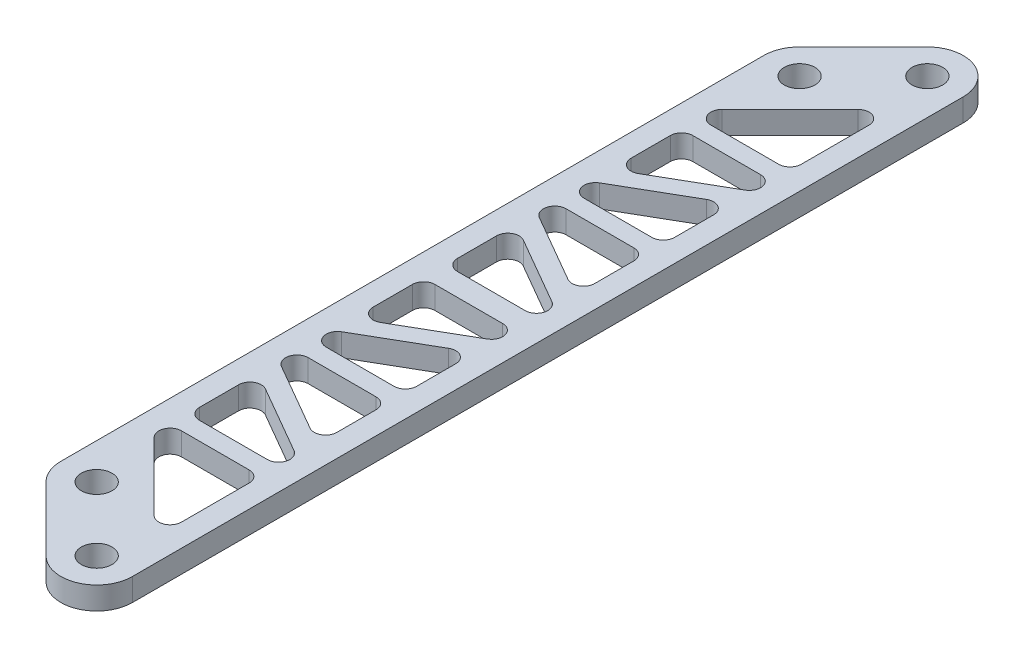
SolidWorks part; units mm, degrees
material "6061-T6 (SS)"
ref_plane "Front Plane" through (0, 0, 0) normal (0, 0, 1) x (1, 0, 0)
ref_plane "Top Plane" through (0, 0, 0) normal (0, 1, 0) x (1, 0, 0)
ref_plane "Right Plane" through (0, 0, 0) normal (1, 0, 0) x (0, 0, -1)
sketch "Sketch1" plane through (0, 0, 0) normal (0, 1, 0) x (1, 0, 0)
  line L0 (0, 0) -> (0, 49.3914)
  line L1 (1.4747, 52.9516) -> (10.4549, 61.9319)
  line L2 (19.05, 58.3717) -> (19.05, 0)
  line L3 (19.05, 0) -> (0, 0)
  line L4 (14.0151, 58.3717) -> (5.0349, 49.3914) construction
  line L5 (5.0349, 49.3914) -> (-44.3565, 0) construction
  line L6 (0, 0) -> (-44.3565, 0) construction
  line L7 (13.165, 49.4393) -> (3.64, 39.9143)
  line L8 (4.7625, 37.2042) -> (14.2875, 37.2042)
  line L9 (15.875, 38.7917) -> (15.875, 48.3167)
  line L13 (4.7625, 38.7917) -> (14.2875, 48.3167) construction
  arc A0 (10.4549, 61.9319) -> (19.05, 58.3717) centre (14.0151, 58.3717) cw
  arc A1 (0, 49.3914) -> (1.4747, 52.9516) centre (5.0349, 49.3914) cw
  circle A2 centre (14.0151, 58.3717) radius 2.0828
  circle A3 centre (5.0349, 49.3914) radius 2.0828
  arc A4 (3.64, 39.9143) -> (4.7625, 37.2042) centre (4.7625, 38.7917) ccw
  arc A5 (14.2875, 37.2042) -> (15.875, 38.7917) centre (14.2875, 38.7917) ccw
  arc A6 (13.165, 49.4393) -> (15.875, 48.3167) centre (14.2875, 48.3167) cw
  point P10 (5.0349, 49.3914)
  point P11 (14.0151, 58.3717)
  dimension "D1" = 19.05
  dimension "D5" = 4.1656
  dimension "D6" = 1.5875
  dimension "D8" = 4.7625
  dimension "D10" = 5.715
  dimension "D2" = 12.7
  dimension "D3" = 69.85
  dimension "D4" = 45
  dimension "D7" = 3.175
  dimension "D9" = 45
extrude "Boss-Extrude1" add sketch "Sketch1" along normal blind 3.175
hole_wizard "#18 (0.1695) Diameter Hole1" positions "Sketch2" profile "Sketch3" hole size "#18" standard "ANSI Inch" end condition through all
sketch "Sketch2" plane through (0, 0, 0) normal (0, -1, 0) x (-1, 0, 0)
  point P0 (-14.0151, 58.3717)
  point P3 (-5.0349, 49.3914)
sketch "Sketch3" plane through (14.0151, 0, -58.3717) normal (1, 0, 0) x (0, 0, -1)
  line L0 (0, 0) -> (0, 3.175)
  line L1 (0, 3.175) -> (2.1526, 3.175)
  line L2 (2.1526, 3.175) -> (2.1526, 0)
  line L5 (2.1526, 0) -> (0, 0)
  line L11 (0, -6.35) -> (0, 107.95) construction
  dimension "Thru Hole Dia." = 4.3053
  dimension "Thru Hole Depth" = 3.175
sketch "Sketch5" plane through (0, 3.175, 0) normal (0, 1, 0) x (1, 0, 0)
  line L0 (14.2875, 34.6642) -> (4.7625, 34.6642)
  line L1 (3.175, 33.0767) -> (3.175, 27.5775)
  line L2 (5.5563, 26.2027) -> (15.0813, 31.7019)
  line L3 (13.4937, 27.8524) -> (3.9687, 22.3532)
  line L4 (4.7625, 19.3909) -> (14.2875, 19.3909)
  line L5 (15.875, 20.9784) -> (15.875, 26.4776)
  line L6 (14.2875, 38.7917) -> (14.2875, 33.0767) construction
  line L7 (4.7625, 33.0767) -> (4.7625, 38.7917) construction
  line L8 (4.7625, 37.2042) -> (14.2875, 37.2042) construction
  line L9 (4.7625, 20.9784) -> (4.7625, 27.5775) construction
  line L10 (14.2875, 26.4776) -> (14.2875, 33.0767) construction
  arc A0 (14.2875, 19.3909) -> (15.875, 20.9784) centre (14.2875, 20.9784) ccw
  arc A1 (13.4937, 27.8524) -> (15.875, 26.4776) centre (14.2875, 26.4776) cw
  arc A2 (3.9687, 22.3532) -> (4.7625, 19.3909) centre (4.7625, 20.9784) ccw
  arc A3 (3.175, 27.5775) -> (5.5563, 26.2027) centre (4.7625, 27.5775) ccw
  arc A4 (14.2875, 34.6642) -> (15.0813, 31.7019) centre (14.2875, 33.0767) cw
  arc A5 (4.7625, 34.6642) -> (3.175, 33.0767) centre (4.7625, 33.0767) ccw
  dimension "D1" = 1.5875
  dimension "D2" = 2.54
  dimension "D3" = 2.54
  dimension "D4" = 60
extrude "Cut-Extrude2" cut sketch "Sketch5" against normal blind 3.175
ref_plane "Plane1" through (0, 0, -18.1209) normal (0, 0, -1) x (-1, 0, 0)
mirror "Mirror2" about plane through (0, 0, -18.1209) normal (0, 0, -1) of "Cut-Extrude2"
mirror "Mirror1" about plane through (19.05, 3.175, 0) normal (0, 0, -1) of "Mirror2", "Cut-Extrude2", "#18 (0.1695) Diameter Hole1", "Boss-Extrude1"
